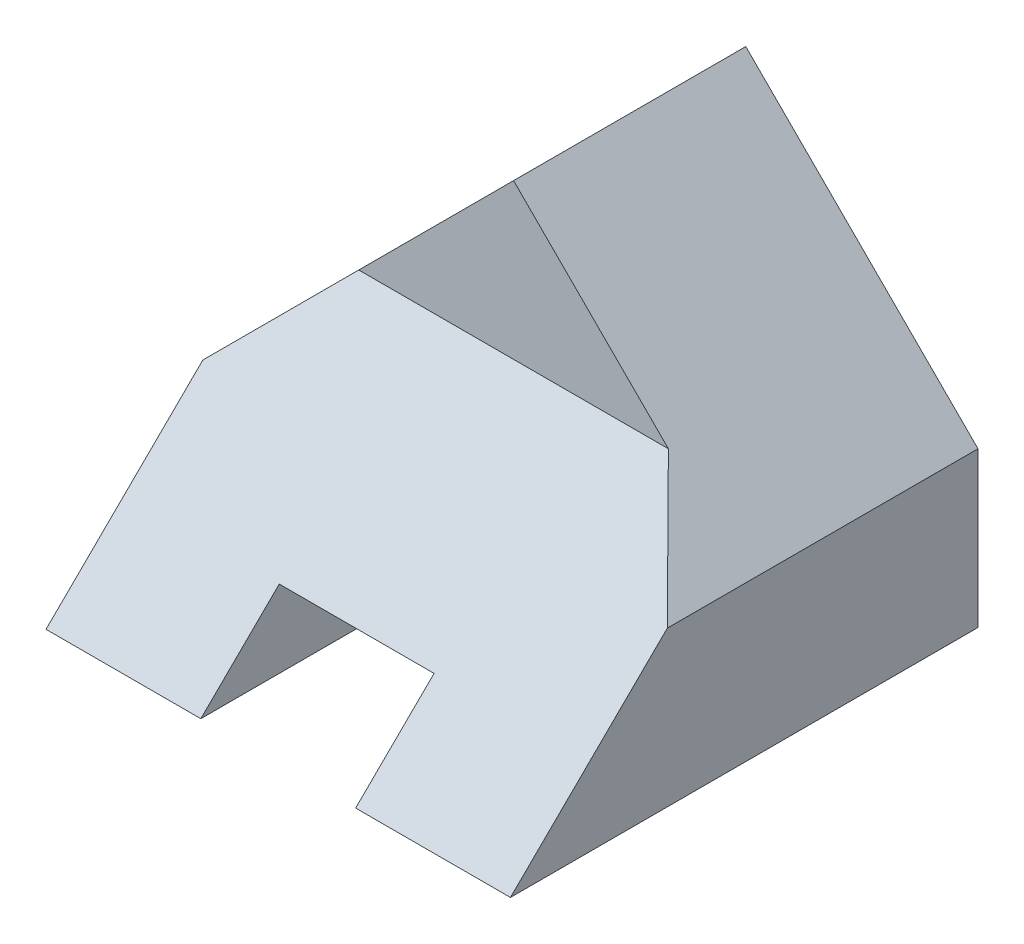
SolidWorks part; units mm, degrees
ref_plane "Front Plane" through (0, 0, 0) normal (0, 0, 1) x (1, 0, 0)
ref_plane "Top Plane" through (0, 0, 0) normal (0, 1, 0) x (1, 0, 0)
ref_plane "Right Plane" through (0, 0, 0) normal (1, 0, 0) x (0, 0, -1)
sketch "Sketch1" plane through (0, 0, 0) normal (0, 0, 1) x (1, 0, 0)
  line L0 (3, 0) -> (-3, 0)
  line L5 (3, 0) -> (3, 2)
  line L6 (3, 2) -> (0, 5)
  line L7 (0, 5) -> (-3, 2)
  line L8 (-3, 2) -> (-3, 0)
  point P5 (0, 0)
  dimension "D1" = 2
  dimension "D2" = 2
  dimension "D3" = 3
  dimension "D4" = 6
  dimension "D5" = 3
  dimension "D6" = 3
extrude "Boss-Extrude1" add sketch "Sketch1" against normal blind 3
sketch "Sketch2" plane through (3, 0, 0) normal (1, 0, 0) x (0, 0, -1)
  line L0 (0, 3) -> (-3.0402, 0)
  line L1 (0, 2) -> (0, 5) construction
  line L2 (-3.0402, 0) -> (0, 0)
  line L3 (0, 0) -> (0, 3)
  dimension "D1" = 2
extrude "Boss-Extrude2" add sketch "Sketch2" against normal blind 6
sketch "Sketch3" plane through (0, 0, 0) normal (0, 0, 1) x (1, 0, 0)
  line L0 (-2, 3) -> (-3, 2)
  line L1 (-3, 2) -> (-3, 3)
  line L2 (-3, 3) -> (-2, 3)
  line L3 (2, 3) -> (3, 2)
  line L4 (3, 2) -> (3, 3)
  line L5 (3, 3) -> (2, 3)
  line L6 (-1, 0) -> (-1, 1)
  line L7 (-3, 0) -> (3, 0) construction
  line L8 (-1, 1) -> (1, 1)
  line L9 (1, 1) -> (1, 0)
  line L10 (1, 0) -> (-1, 0)
  dimension "D1" = 1
  dimension "D2" = 2
  dimension "D3" = 1
extrude "Cut-Extrude1" cut sketch "Sketch3" along normal blind 6
